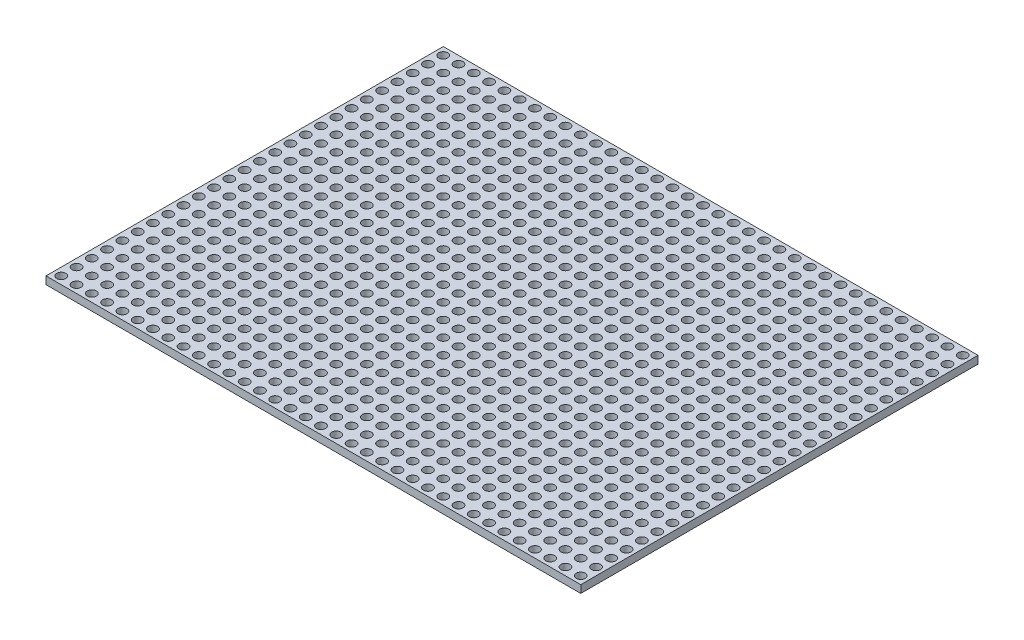
SolidWorks part; units mm, degrees
ref_plane "Front Plane" through (0, 0, 0) normal (0, 0, 1) x (1, 0, 0)
ref_plane "Top Plane" through (0, 0, 0) normal (0, 1, 0) x (1, 0, 0)
ref_plane "Right Plane" through (0, 0, 0) normal (1, 0, 0) x (0, 0, -1)
sketch "Sketch1" plane through (0, 0, 0) normal (0, 1, 0) x (1, 0, 0)
  line L1 (-35, -26) -> (35, -26)
  line L2 (-35, -26) -> (-35, 26)
  line L3 (-35, 26) -> (35, 26)
  line L4 (35, -26) -> (35, 26)
  line L5 (-35, -26) -> (35, 26) construction
  line L6 (-35, 26) -> (35, -26) construction
  circle A0 centre (-34, 25) radius 0.5928
  circle A1 centre (-32, 25) radius 0.5928
  circle A2 centre (-30, 25) radius 0.5928
  circle A3 centre (-28, 25) radius 0.5928
  circle A4 centre (-26, 25) radius 0.5928
  circle A5 centre (-24, 25) radius 0.5928
  circle A6 centre (-22, 25) radius 0.5928
  circle A7 centre (-20, 25) radius 0.5928
  circle A8 centre (-18, 25) radius 0.5928
  circle A9 centre (-16, 25) radius 0.5928
  circle A10 centre (-14, 25) radius 0.5928
  circle A11 centre (-12, 25) radius 0.5928
  circle A12 centre (-10, 25) radius 0.5928
  circle A13 centre (-8, 25) radius 0.5928
  circle A14 centre (-6, 25) radius 0.5928
  circle A15 centre (-4, 25) radius 0.5928
  circle A16 centre (-2, 25) radius 0.5928
  circle A17 centre (0, 25) radius 0.5928
  circle A18 centre (2, 25) radius 0.5928
  circle A19 centre (4, 25) radius 0.5928
  circle A20 centre (6, 25) radius 0.5928
  circle A21 centre (8, 25) radius 0.5928
  circle A22 centre (10, 25) radius 0.5928
  circle A23 centre (12, 25) radius 0.5928
  circle A24 centre (14, 25) radius 0.5928
  circle A25 centre (16, 25) radius 0.5928
  circle A26 centre (18, 25) radius 0.5928
  circle A27 centre (20, 25) radius 0.5928
  circle A28 centre (22, 25) radius 0.5928
  circle A29 centre (24, 25) radius 0.5928
  circle A30 centre (26, 25) radius 0.5928
  circle A31 centre (28, 25) radius 0.5928
  circle A32 centre (30, 25) radius 0.5928
  circle A33 centre (32, 25) radius 0.5928
  circle A34 centre (34, 25) radius 0.5928
  circle A35 centre (-32, 23) radius 0.5928
  circle A36 centre (-30, 23) radius 0.5928
  circle A37 centre (-28, 23) radius 0.5928
  circle A38 centre (-26, 23) radius 0.5928
  circle A39 centre (-24, 23) radius 0.5928
  circle A40 centre (-22, 23) radius 0.5928
  circle A41 centre (-20, 23) radius 0.5928
  circle A42 centre (-18, 23) radius 0.5928
  circle A43 centre (-16, 23) radius 0.5928
  circle A44 centre (-14, 23) radius 0.5928
  circle A45 centre (-12, 23) radius 0.5928
  circle A46 centre (-10, 23) radius 0.5928
  circle A47 centre (-8, 23) radius 0.5928
  circle A48 centre (-6, 23) radius 0.5928
  circle A49 centre (-4, 23) radius 0.5928
  circle A50 centre (-2, 23) radius 0.5928
  circle A51 centre (0, 23) radius 0.5928
  circle A52 centre (2, 23) radius 0.5928
  circle A53 centre (4, 23) radius 0.5928
  circle A54 centre (6, 23) radius 0.5928
  circle A55 centre (8, 23) radius 0.5928
  circle A56 centre (10, 23) radius 0.5928
  circle A57 centre (12, 23) radius 0.5928
  circle A58 centre (14, 23) radius 0.5928
  circle A59 centre (16, 23) radius 0.5928
  circle A60 centre (18, 23) radius 0.5928
  circle A61 centre (20, 23) radius 0.5928
  circle A62 centre (22, 23) radius 0.5928
  circle A63 centre (24, 23) radius 0.5928
  circle A64 centre (26, 23) radius 0.5928
  circle A65 centre (28, 23) radius 0.5928
  circle A66 centre (30, 23) radius 0.5928
  circle A67 centre (32, 23) radius 0.5928
  circle A68 centre (34, 23) radius 0.5928
  circle A69 centre (-32, 21) radius 0.5928
  circle A70 centre (-30, 21) radius 0.5928
  circle A71 centre (-28, 21) radius 0.5928
  circle A72 centre (-26, 21) radius 0.5928
  circle A73 centre (-24, 21) radius 0.5928
  circle A74 centre (-22, 21) radius 0.5928
  circle A75 centre (-20, 21) radius 0.5928
  circle A76 centre (-18, 21) radius 0.5928
  circle A77 centre (-16, 21) radius 0.5928
  circle A78 centre (-14, 21) radius 0.5928
  circle A79 centre (-12, 21) radius 0.5928
  circle A80 centre (-10, 21) radius 0.5928
  circle A81 centre (-8, 21) radius 0.5928
  circle A82 centre (-6, 21) radius 0.5928
  circle A83 centre (-4, 21) radius 0.5928
  circle A84 centre (-2, 21) radius 0.5928
  circle A85 centre (0, 21) radius 0.5928
  circle A86 centre (2, 21) radius 0.5928
  circle A87 centre (4, 21) radius 0.5928
  circle A88 centre (6, 21) radius 0.5928
  circle A89 centre (8, 21) radius 0.5928
  circle A90 centre (10, 21) radius 0.5928
  circle A91 centre (12, 21) radius 0.5928
  circle A92 centre (14, 21) radius 0.5928
  circle A93 centre (16, 21) radius 0.5928
  circle A94 centre (18, 21) radius 0.5928
  circle A95 centre (20, 21) radius 0.5928
  circle A96 centre (22, 21) radius 0.5928
  circle A97 centre (24, 21) radius 0.5928
  circle A98 centre (26, 21) radius 0.5928
  circle A99 centre (28, 21) radius 0.5928
  circle A100 centre (30, 21) radius 0.5928
  circle A101 centre (32, 21) radius 0.5928
  circle A102 centre (34, 21) radius 0.5928
  circle A103 centre (-32, 19) radius 0.5928
  circle A104 centre (-30, 19) radius 0.5928
  circle A105 centre (-28, 19) radius 0.5928
  circle A106 centre (-26, 19) radius 0.5928
  circle A107 centre (-24, 19) radius 0.5928
  circle A108 centre (-22, 19) radius 0.5928
  circle A109 centre (-20, 19) radius 0.5928
  circle A110 centre (-18, 19) radius 0.5928
  circle A111 centre (-16, 19) radius 0.5928
  circle A112 centre (-14, 19) radius 0.5928
  circle A113 centre (-12, 19) radius 0.5928
  circle A114 centre (-10, 19) radius 0.5928
  circle A115 centre (-8, 19) radius 0.5928
  circle A116 centre (-6, 19) radius 0.5928
  circle A117 centre (-4, 19) radius 0.5928
  circle A118 centre (-2, 19) radius 0.5928
  circle A119 centre (0, 19) radius 0.5928
  circle A120 centre (2, 19) radius 0.5928
  circle A121 centre (4, 19) radius 0.5928
  circle A122 centre (6, 19) radius 0.5928
  circle A123 centre (8, 19) radius 0.5928
  circle A124 centre (10, 19) radius 0.5928
  circle A125 centre (12, 19) radius 0.5928
  circle A126 centre (14, 19) radius 0.5928
  circle A127 centre (16, 19) radius 0.5928
  circle A128 centre (18, 19) radius 0.5928
  circle A129 centre (20, 19) radius 0.5928
  circle A130 centre (22, 19) radius 0.5928
  circle A131 centre (24, 19) radius 0.5928
  circle A132 centre (26, 19) radius 0.5928
  circle A133 centre (28, 19) radius 0.5928
  circle A134 centre (30, 19) radius 0.5928
  circle A135 centre (32, 19) radius 0.5928
  circle A136 centre (34, 19) radius 0.5928
  circle A137 centre (-32, 17) radius 0.5928
  circle A138 centre (-30, 17) radius 0.5928
  circle A139 centre (-28, 17) radius 0.5928
  circle A140 centre (-26, 17) radius 0.5928
  circle A141 centre (-24, 17) radius 0.5928
  circle A142 centre (-22, 17) radius 0.5928
  circle A143 centre (-20, 17) radius 0.5928
  circle A144 centre (-18, 17) radius 0.5928
  circle A145 centre (-16, 17) radius 0.5928
  circle A146 centre (-14, 17) radius 0.5928
  circle A147 centre (-12, 17) radius 0.5928
  circle A148 centre (-10, 17) radius 0.5928
  circle A149 centre (-8, 17) radius 0.5928
  circle A150 centre (-6, 17) radius 0.5928
  circle A151 centre (-4, 17) radius 0.5928
  circle A152 centre (-2, 17) radius 0.5928
  circle A153 centre (0, 17) radius 0.5928
  circle A154 centre (2, 17) radius 0.5928
  circle A155 centre (4, 17) radius 0.5928
  circle A156 centre (6, 17) radius 0.5928
  circle A157 centre (8, 17) radius 0.5928
  circle A158 centre (10, 17) radius 0.5928
  circle A159 centre (12, 17) radius 0.5928
  circle A160 centre (14, 17) radius 0.5928
  circle A161 centre (16, 17) radius 0.5928
  circle A162 centre (18, 17) radius 0.5928
  circle A163 centre (20, 17) radius 0.5928
  circle A164 centre (22, 17) radius 0.5928
  circle A165 centre (24, 17) radius 0.5928
  circle A166 centre (26, 17) radius 0.5928
  circle A167 centre (28, 17) radius 0.5928
  circle A168 centre (30, 17) radius 0.5928
  circle A169 centre (32, 17) radius 0.5928
  circle A170 centre (34, 17) radius 0.5928
  circle A171 centre (-32, 15) radius 0.5928
  circle A172 centre (-30, 15) radius 0.5928
  circle A173 centre (-28, 15) radius 0.5928
  circle A174 centre (-26, 15) radius 0.5928
  circle A175 centre (-24, 15) radius 0.5928
  circle A176 centre (-22, 15) radius 0.5928
  circle A177 centre (-20, 15) radius 0.5928
  circle A178 centre (-18, 15) radius 0.5928
  circle A179 centre (-16, 15) radius 0.5928
  circle A180 centre (-14, 15) radius 0.5928
  circle A181 centre (-12, 15) radius 0.5928
  circle A182 centre (-10, 15) radius 0.5928
  circle A183 centre (-8, 15) radius 0.5928
  circle A184 centre (-6, 15) radius 0.5928
  circle A185 centre (-4, 15) radius 0.5928
  circle A186 centre (-2, 15) radius 0.5928
  circle A187 centre (0, 15) radius 0.5928
  circle A188 centre (2, 15) radius 0.5928
  circle A189 centre (4, 15) radius 0.5928
  circle A190 centre (6, 15) radius 0.5928
  circle A191 centre (8, 15) radius 0.5928
  circle A192 centre (10, 15) radius 0.5928
  circle A193 centre (12, 15) radius 0.5928
  circle A194 centre (14, 15) radius 0.5928
  circle A195 centre (16, 15) radius 0.5928
  circle A196 centre (18, 15) radius 0.5928
  circle A197 centre (20, 15) radius 0.5928
  circle A198 centre (22, 15) radius 0.5928
  circle A199 centre (24, 15) radius 0.5928
  circle A200 centre (26, 15) radius 0.5928
  circle A201 centre (28, 15) radius 0.5928
  circle A202 centre (30, 15) radius 0.5928
  circle A203 centre (32, 15) radius 0.5928
  circle A204 centre (34, 15) radius 0.5928
  circle A205 centre (-32, 13) radius 0.5928
  circle A206 centre (-30, 13) radius 0.5928
  circle A207 centre (-28, 13) radius 0.5928
  circle A208 centre (-26, 13) radius 0.5928
  circle A209 centre (-24, 13) radius 0.5928
  circle A210 centre (-22, 13) radius 0.5928
  circle A211 centre (-20, 13) radius 0.5928
  circle A212 centre (-18, 13) radius 0.5928
  circle A213 centre (-16, 13) radius 0.5928
  circle A214 centre (-14, 13) radius 0.5928
  circle A215 centre (-12, 13) radius 0.5928
  circle A216 centre (-10, 13) radius 0.5928
  circle A217 centre (-8, 13) radius 0.5928
  circle A218 centre (-6, 13) radius 0.5928
  circle A219 centre (-4, 13) radius 0.5928
  circle A220 centre (-2, 13) radius 0.5928
  circle A221 centre (0, 13) radius 0.5928
  circle A222 centre (2, 13) radius 0.5928
  circle A223 centre (4, 13) radius 0.5928
  circle A224 centre (6, 13) radius 0.5928
  circle A225 centre (8, 13) radius 0.5928
  circle A226 centre (10, 13) radius 0.5928
  circle A227 centre (12, 13) radius 0.5928
  circle A228 centre (14, 13) radius 0.5928
  circle A229 centre (16, 13) radius 0.5928
  circle A230 centre (18, 13) radius 0.5928
  circle A231 centre (20, 13) radius 0.5928
  circle A232 centre (22, 13) radius 0.5928
  circle A233 centre (24, 13) radius 0.5928
  circle A234 centre (26, 13) radius 0.5928
  circle A235 centre (28, 13) radius 0.5928
  circle A236 centre (30, 13) radius 0.5928
  circle A237 centre (32, 13) radius 0.5928
  circle A238 centre (34, 13) radius 0.5928
  circle A239 centre (-32, 11) radius 0.5928
  circle A240 centre (-30, 11) radius 0.5928
  circle A241 centre (-28, 11) radius 0.5928
  circle A242 centre (-26, 11) radius 0.5928
  circle A243 centre (-24, 11) radius 0.5928
  circle A244 centre (-22, 11) radius 0.5928
  circle A245 centre (-20, 11) radius 0.5928
  circle A246 centre (-18, 11) radius 0.5928
  circle A247 centre (-16, 11) radius 0.5928
  circle A248 centre (-14, 11) radius 0.5928
  circle A249 centre (-12, 11) radius 0.5928
  circle A250 centre (-10, 11) radius 0.5928
  circle A251 centre (-8, 11) radius 0.5928
  circle A252 centre (-6, 11) radius 0.5928
  circle A253 centre (-4, 11) radius 0.5928
  circle A254 centre (-2, 11) radius 0.5928
  circle A255 centre (0, 11) radius 0.5928
  circle A256 centre (2, 11) radius 0.5928
  circle A257 centre (4, 11) radius 0.5928
  circle A258 centre (6, 11) radius 0.5928
  circle A259 centre (8, 11) radius 0.5928
  circle A260 centre (10, 11) radius 0.5928
  circle A261 centre (12, 11) radius 0.5928
  circle A262 centre (14, 11) radius 0.5928
  circle A263 centre (16, 11) radius 0.5928
  circle A264 centre (18, 11) radius 0.5928
  circle A265 centre (20, 11) radius 0.5928
  circle A266 centre (22, 11) radius 0.5928
  circle A267 centre (24, 11) radius 0.5928
  circle A268 centre (26, 11) radius 0.5928
  circle A269 centre (28, 11) radius 0.5928
  circle A270 centre (30, 11) radius 0.5928
  circle A271 centre (32, 11) radius 0.5928
  circle A272 centre (34, 11) radius 0.5928
  circle A273 centre (-32, 9) radius 0.5928
  circle A274 centre (-30, 9) radius 0.5928
  circle A275 centre (-28, 9) radius 0.5928
  circle A276 centre (-26, 9) radius 0.5928
  circle A277 centre (-24, 9) radius 0.5928
  circle A278 centre (-22, 9) radius 0.5928
  circle A279 centre (-20, 9) radius 0.5928
  circle A280 centre (-18, 9) radius 0.5928
  circle A281 centre (-16, 9) radius 0.5928
  circle A282 centre (-14, 9) radius 0.5928
  circle A283 centre (-12, 9) radius 0.5928
  circle A284 centre (-10, 9) radius 0.5928
  circle A285 centre (-8, 9) radius 0.5928
  circle A286 centre (-6, 9) radius 0.5928
  circle A287 centre (-4, 9) radius 0.5928
  circle A288 centre (-2, 9) radius 0.5928
  circle A289 centre (0, 9) radius 0.5928
  circle A290 centre (2, 9) radius 0.5928
  circle A291 centre (4, 9) radius 0.5928
  circle A292 centre (6, 9) radius 0.5928
  circle A293 centre (8, 9) radius 0.5928
  circle A294 centre (10, 9) radius 0.5928
  circle A295 centre (12, 9) radius 0.5928
  circle A296 centre (14, 9) radius 0.5928
  circle A297 centre (16, 9) radius 0.5928
  circle A298 centre (18, 9) radius 0.5928
  circle A299 centre (20, 9) radius 0.5928
  circle A300 centre (22, 9) radius 0.5928
  circle A301 centre (24, 9) radius 0.5928
  circle A302 centre (26, 9) radius 0.5928
  circle A303 centre (28, 9) radius 0.5928
  circle A304 centre (30, 9) radius 0.5928
  circle A305 centre (32, 9) radius 0.5928
  circle A306 centre (34, 9) radius 0.5928
  circle A307 centre (-32, 7) radius 0.5928
  circle A308 centre (-30, 7) radius 0.5928
  circle A309 centre (-28, 7) radius 0.5928
  circle A310 centre (-26, 7) radius 0.5928
  circle A311 centre (-24, 7) radius 0.5928
  circle A312 centre (-22, 7) radius 0.5928
  circle A313 centre (-20, 7) radius 0.5928
  circle A314 centre (-18, 7) radius 0.5928
  circle A315 centre (-16, 7) radius 0.5928
  circle A316 centre (-14, 7) radius 0.5928
  circle A317 centre (-12, 7) radius 0.5928
  circle A318 centre (-10, 7) radius 0.5928
  circle A319 centre (-8, 7) radius 0.5928
  circle A320 centre (-6, 7) radius 0.5928
  circle A321 centre (-4, 7) radius 0.5928
  circle A322 centre (-2, 7) radius 0.5928
  circle A323 centre (0, 7) radius 0.5928
  circle A324 centre (2, 7) radius 0.5928
  circle A325 centre (4, 7) radius 0.5928
  circle A326 centre (6, 7) radius 0.5928
  circle A327 centre (8, 7) radius 0.5928
  circle A328 centre (10, 7) radius 0.5928
  circle A329 centre (12, 7) radius 0.5928
  circle A330 centre (14, 7) radius 0.5928
  circle A331 centre (16, 7) radius 0.5928
  circle A332 centre (18, 7) radius 0.5928
  circle A333 centre (20, 7) radius 0.5928
  circle A334 centre (22, 7) radius 0.5928
  circle A335 centre (24, 7) radius 0.5928
  circle A336 centre (26, 7) radius 0.5928
  circle A337 centre (28, 7) radius 0.5928
  circle A338 centre (30, 7) radius 0.5928
  circle A339 centre (32, 7) radius 0.5928
  circle A340 centre (34, 7) radius 0.5928
  circle A341 centre (-32, 5) radius 0.5928
  circle A342 centre (-30, 5) radius 0.5928
  circle A343 centre (-28, 5) radius 0.5928
  circle A344 centre (-26, 5) radius 0.5928
  circle A345 centre (-24, 5) radius 0.5928
  circle A346 centre (-22, 5) radius 0.5928
  circle A347 centre (-20, 5) radius 0.5928
  circle A348 centre (-18, 5) radius 0.5928
  circle A349 centre (-16, 5) radius 0.5928
  circle A350 centre (-14, 5) radius 0.5928
  circle A351 centre (-12, 5) radius 0.5928
  circle A352 centre (-10, 5) radius 0.5928
  circle A353 centre (-8, 5) radius 0.5928
  circle A354 centre (-6, 5) radius 0.5928
  circle A355 centre (-4, 5) radius 0.5928
  circle A356 centre (-2, 5) radius 0.5928
  circle A357 centre (0, 5) radius 0.5928
  circle A358 centre (2, 5) radius 0.5928
  circle A359 centre (4, 5) radius 0.5928
  circle A360 centre (6, 5) radius 0.5928
  circle A361 centre (8, 5) radius 0.5928
  circle A362 centre (10, 5) radius 0.5928
  circle A363 centre (12, 5) radius 0.5928
  circle A364 centre (14, 5) radius 0.5928
  circle A365 centre (16, 5) radius 0.5928
  circle A366 centre (18, 5) radius 0.5928
  circle A367 centre (20, 5) radius 0.5928
  circle A368 centre (22, 5) radius 0.5928
  circle A369 centre (24, 5) radius 0.5928
  circle A370 centre (26, 5) radius 0.5928
  circle A371 centre (28, 5) radius 0.5928
  circle A372 centre (30, 5) radius 0.5928
  circle A373 centre (32, 5) radius 0.5928
  circle A374 centre (34, 5) radius 0.5928
  circle A375 centre (-32, 3) radius 0.5928
  circle A376 centre (-30, 3) radius 0.5928
  circle A377 centre (-28, 3) radius 0.5928
  circle A378 centre (-26, 3) radius 0.5928
  circle A379 centre (-24, 3) radius 0.5928
  circle A380 centre (-22, 3) radius 0.5928
  circle A381 centre (-20, 3) radius 0.5928
  circle A382 centre (-18, 3) radius 0.5928
  circle A383 centre (-16, 3) radius 0.5928
  circle A384 centre (-14, 3) radius 0.5928
  circle A385 centre (-12, 3) radius 0.5928
  circle A386 centre (-10, 3) radius 0.5928
  circle A387 centre (-8, 3) radius 0.5928
  circle A388 centre (-6, 3) radius 0.5928
  circle A389 centre (-4, 3) radius 0.5928
  circle A390 centre (-2, 3) radius 0.5928
  circle A391 centre (0, 3) radius 0.5928
  circle A392 centre (2, 3) radius 0.5928
  circle A393 centre (4, 3) radius 0.5928
  circle A394 centre (6, 3) radius 0.5928
  circle A395 centre (8, 3) radius 0.5928
  circle A396 centre (10, 3) radius 0.5928
  circle A397 centre (12, 3) radius 0.5928
  circle A398 centre (14, 3) radius 0.5928
  circle A399 centre (16, 3) radius 0.5928
  circle A400 centre (18, 3) radius 0.5928
  circle A401 centre (20, 3) radius 0.5928
  circle A402 centre (22, 3) radius 0.5928
  circle A403 centre (24, 3) radius 0.5928
  circle A404 centre (26, 3) radius 0.5928
  circle A405 centre (28, 3) radius 0.5928
  circle A406 centre (30, 3) radius 0.5928
  circle A407 centre (32, 3) radius 0.5928
  circle A408 centre (34, 3) radius 0.5928
  circle A409 centre (-32, 1) radius 0.5928
  circle A410 centre (-30, 1) radius 0.5928
  circle A411 centre (-28, 1) radius 0.5928
  circle A412 centre (-26, 1) radius 0.5928
  circle A413 centre (-24, 1) radius 0.5928
  circle A414 centre (-22, 1) radius 0.5928
  circle A415 centre (-20, 1) radius 0.5928
  circle A416 centre (-18, 1) radius 0.5928
  circle A417 centre (-16, 1) radius 0.5928
  circle A418 centre (-14, 1) radius 0.5928
  circle A419 centre (-12, 1) radius 0.5928
  circle A420 centre (-10, 1) radius 0.5928
  circle A421 centre (-8, 1) radius 0.5928
  circle A422 centre (-6, 1) radius 0.5928
  circle A423 centre (-4, 1) radius 0.5928
  circle A424 centre (-2, 1) radius 0.5928
  circle A425 centre (0, 1) radius 0.5928
  circle A426 centre (2, 1) radius 0.5928
  circle A427 centre (4, 1) radius 0.5928
  circle A428 centre (6, 1) radius 0.5928
  circle A429 centre (8, 1) radius 0.5928
  circle A430 centre (10, 1) radius 0.5928
  circle A431 centre (12, 1) radius 0.5928
  circle A432 centre (14, 1) radius 0.5928
  circle A433 centre (16, 1) radius 0.5928
  circle A434 centre (18, 1) radius 0.5928
  circle A435 centre (20, 1) radius 0.5928
  circle A436 centre (22, 1) radius 0.5928
  circle A437 centre (24, 1) radius 0.5928
  circle A438 centre (26, 1) radius 0.5928
  circle A439 centre (28, 1) radius 0.5928
  circle A440 centre (30, 1) radius 0.5928
  circle A441 centre (32, 1) radius 0.5928
  circle A442 centre (34, 1) radius 0.5928
  circle A443 centre (-32, -1) radius 0.5928
  circle A444 centre (-30, -1) radius 0.5928
  circle A445 centre (-28, -1) radius 0.5928
  circle A446 centre (-26, -1) radius 0.5928
  circle A447 centre (-24, -1) radius 0.5928
  circle A448 centre (-22, -1) radius 0.5928
  circle A449 centre (-20, -1) radius 0.5928
  circle A450 centre (-18, -1) radius 0.5928
  circle A451 centre (-16, -1) radius 0.5928
  circle A452 centre (-14, -1) radius 0.5928
  circle A453 centre (-12, -1) radius 0.5928
  circle A454 centre (-10, -1) radius 0.5928
  circle A455 centre (-8, -1) radius 0.5928
  circle A456 centre (-6, -1) radius 0.5928
  circle A457 centre (-4, -1) radius 0.5928
  circle A458 centre (-2, -1) radius 0.5928
  circle A459 centre (0, -1) radius 0.5928
  circle A460 centre (2, -1) radius 0.5928
  circle A461 centre (4, -1) radius 0.5928
  circle A462 centre (6, -1) radius 0.5928
  circle A463 centre (8, -1) radius 0.5928
  circle A464 centre (10, -1) radius 0.5928
  circle A465 centre (12, -1) radius 0.5928
  circle A466 centre (14, -1) radius 0.5928
  circle A467 centre (16, -1) radius 0.5928
  circle A468 centre (18, -1) radius 0.5928
  circle A469 centre (20, -1) radius 0.5928
  circle A470 centre (22, -1) radius 0.5928
  circle A471 centre (24, -1) radius 0.5928
  circle A472 centre (26, -1) radius 0.5928
  circle A473 centre (28, -1) radius 0.5928
  circle A474 centre (30, -1) radius 0.5928
  circle A475 centre (32, -1) radius 0.5928
  circle A476 centre (34, -1) radius 0.5928
  circle A477 centre (-32, -3) radius 0.5928
  circle A478 centre (-30, -3) radius 0.5928
  circle A479 centre (-28, -3) radius 0.5928
  circle A480 centre (-26, -3) radius 0.5928
  circle A481 centre (-24, -3) radius 0.5928
  circle A482 centre (-22, -3) radius 0.5928
  circle A483 centre (-20, -3) radius 0.5928
  circle A484 centre (-18, -3) radius 0.5928
  circle A485 centre (-16, -3) radius 0.5928
  circle A486 centre (-14, -3) radius 0.5928
  circle A487 centre (-12, -3) radius 0.5928
  circle A488 centre (-10, -3) radius 0.5928
  circle A489 centre (-8, -3) radius 0.5928
  circle A490 centre (-6, -3) radius 0.5928
  circle A491 centre (-4, -3) radius 0.5928
  circle A492 centre (-2, -3) radius 0.5928
  circle A493 centre (0, -3) radius 0.5928
  circle A494 centre (2, -3) radius 0.5928
  circle A495 centre (4, -3) radius 0.5928
  circle A496 centre (6, -3) radius 0.5928
  circle A497 centre (8, -3) radius 0.5928
  circle A498 centre (10, -3) radius 0.5928
  circle A499 centre (12, -3) radius 0.5928
  circle A500 centre (14, -3) radius 0.5928
  circle A501 centre (16, -3) radius 0.5928
  circle A502 centre (18, -3) radius 0.5928
  circle A503 centre (20, -3) radius 0.5928
  circle A504 centre (22, -3) radius 0.5928
  circle A505 centre (24, -3) radius 0.5928
  circle A506 centre (26, -3) radius 0.5928
  circle A507 centre (28, -3) radius 0.5928
  circle A508 centre (30, -3) radius 0.5928
  circle A509 centre (32, -3) radius 0.5928
  circle A510 centre (34, -3) radius 0.5928
  circle A511 centre (-32, -5) radius 0.5928
  circle A512 centre (-30, -5) radius 0.5928
  circle A513 centre (-28, -5) radius 0.5928
  circle A514 centre (-26, -5) radius 0.5928
  circle A515 centre (-24, -5) radius 0.5928
  circle A516 centre (-22, -5) radius 0.5928
  circle A517 centre (-20, -5) radius 0.5928
  circle A518 centre (-18, -5) radius 0.5928
  circle A519 centre (-16, -5) radius 0.5928
  circle A520 centre (-14, -5) radius 0.5928
  circle A521 centre (-12, -5) radius 0.5928
  circle A522 centre (-10, -5) radius 0.5928
  circle A523 centre (-8, -5) radius 0.5928
  circle A524 centre (-6, -5) radius 0.5928
  circle A525 centre (-4, -5) radius 0.5928
  circle A526 centre (-2, -5) radius 0.5928
  circle A527 centre (0, -5) radius 0.5928
  circle A528 centre (2, -5) radius 0.5928
  circle A529 centre (4, -5) radius 0.5928
  circle A530 centre (6, -5) radius 0.5928
  circle A531 centre (8, -5) radius 0.5928
  circle A532 centre (10, -5) radius 0.5928
  circle A533 centre (12, -5) radius 0.5928
  circle A534 centre (14, -5) radius 0.5928
  circle A535 centre (16, -5) radius 0.5928
  circle A536 centre (18, -5) radius 0.5928
  circle A537 centre (20, -5) radius 0.5928
  circle A538 centre (22, -5) radius 0.5928
  circle A539 centre (24, -5) radius 0.5928
  circle A540 centre (26, -5) radius 0.5928
  circle A541 centre (28, -5) radius 0.5928
  circle A542 centre (30, -5) radius 0.5928
  circle A543 centre (32, -5) radius 0.5928
  circle A544 centre (34, -5) radius 0.5928
  circle A545 centre (-32, -7) radius 0.5928
  circle A546 centre (-30, -7) radius 0.5928
  circle A547 centre (-28, -7) radius 0.5928
  circle A548 centre (-26, -7) radius 0.5928
  circle A549 centre (-24, -7) radius 0.5928
  circle A550 centre (-22, -7) radius 0.5928
  circle A551 centre (-20, -7) radius 0.5928
  circle A552 centre (-18, -7) radius 0.5928
  circle A553 centre (-16, -7) radius 0.5928
  circle A554 centre (-14, -7) radius 0.5928
  circle A555 centre (-12, -7) radius 0.5928
  circle A556 centre (-10, -7) radius 0.5928
  circle A557 centre (-8, -7) radius 0.5928
  circle A558 centre (-6, -7) radius 0.5928
  circle A559 centre (-4, -7) radius 0.5928
  circle A560 centre (-2, -7) radius 0.5928
  circle A561 centre (0, -7) radius 0.5928
  circle A562 centre (2, -7) radius 0.5928
  circle A563 centre (4, -7) radius 0.5928
  circle A564 centre (6, -7) radius 0.5928
  circle A565 centre (8, -7) radius 0.5928
  circle A566 centre (10, -7) radius 0.5928
  circle A567 centre (12, -7) radius 0.5928
  circle A568 centre (14, -7) radius 0.5928
  circle A569 centre (16, -7) radius 0.5928
  circle A570 centre (18, -7) radius 0.5928
  circle A571 centre (20, -7) radius 0.5928
  circle A572 centre (22, -7) radius 0.5928
  circle A573 centre (24, -7) radius 0.5928
  circle A574 centre (26, -7) radius 0.5928
  circle A575 centre (28, -7) radius 0.5928
  circle A576 centre (30, -7) radius 0.5928
  circle A577 centre (32, -7) radius 0.5928
  circle A578 centre (34, -7) radius 0.5928
  circle A579 centre (-32, -9) radius 0.5928
  circle A580 centre (-30, -9) radius 0.5928
  circle A581 centre (-28, -9) radius 0.5928
  circle A582 centre (-26, -9) radius 0.5928
  circle A583 centre (-24, -9) radius 0.5928
  circle A584 centre (-22, -9) radius 0.5928
  circle A585 centre (-20, -9) radius 0.5928
  circle A586 centre (-18, -9) radius 0.5928
  circle A587 centre (-16, -9) radius 0.5928
  circle A588 centre (-14, -9) radius 0.5928
  circle A589 centre (-12, -9) radius 0.5928
  circle A590 centre (-10, -9) radius 0.5928
  circle A591 centre (-8, -9) radius 0.5928
  circle A592 centre (-6, -9) radius 0.5928
  circle A593 centre (-4, -9) radius 0.5928
  circle A594 centre (-2, -9) radius 0.5928
  circle A595 centre (0, -9) radius 0.5928
  circle A596 centre (2, -9) radius 0.5928
  circle A597 centre (4, -9) radius 0.5928
  circle A598 centre (6, -9) radius 0.5928
  circle A599 centre (8, -9) radius 0.5928
  circle A600 centre (10, -9) radius 0.5928
  circle A601 centre (12, -9) radius 0.5928
  circle A602 centre (14, -9) radius 0.5928
  circle A603 centre (16, -9) radius 0.5928
  circle A604 centre (18, -9) radius 0.5928
  circle A605 centre (20, -9) radius 0.5928
  circle A606 centre (22, -9) radius 0.5928
  circle A607 centre (24, -9) radius 0.5928
  circle A608 centre (26, -9) radius 0.5928
  circle A609 centre (28, -9) radius 0.5928
  circle A610 centre (30, -9) radius 0.5928
  circle A611 centre (32, -9) radius 0.5928
  circle A612 centre (34, -9) radius 0.5928
  circle A613 centre (-32, -11) radius 0.5928
  circle A614 centre (-30, -11) radius 0.5928
  circle A615 centre (-28, -11) radius 0.5928
  circle A616 centre (-26, -11) radius 0.5928
  circle A617 centre (-24, -11) radius 0.5928
  circle A618 centre (-22, -11) radius 0.5928
  circle A619 centre (-20, -11) radius 0.5928
  circle A620 centre (-18, -11) radius 0.5928
  circle A621 centre (-16, -11) radius 0.5928
  circle A622 centre (-14, -11) radius 0.5928
  circle A623 centre (-12, -11) radius 0.5928
  circle A624 centre (-10, -11) radius 0.5928
  circle A625 centre (-8, -11) radius 0.5928
  circle A626 centre (-6, -11) radius 0.5928
  circle A627 centre (-4, -11) radius 0.5928
  circle A628 centre (-2, -11) radius 0.5928
  circle A629 centre (0, -11) radius 0.5928
  circle A630 centre (2, -11) radius 0.5928
  circle A631 centre (4, -11) radius 0.5928
  circle A632 centre (6, -11) radius 0.5928
  circle A633 centre (8, -11) radius 0.5928
  circle A634 centre (10, -11) radius 0.5928
  circle A635 centre (12, -11) radius 0.5928
  circle A636 centre (14, -11) radius 0.5928
  circle A637 centre (16, -11) radius 0.5928
  circle A638 centre (18, -11) radius 0.5928
  circle A639 centre (20, -11) radius 0.5928
  circle A640 centre (22, -11) radius 0.5928
  circle A641 centre (24, -11) radius 0.5928
  circle A642 centre (26, -11) radius 0.5928
  circle A643 centre (28, -11) radius 0.5928
  circle A644 centre (30, -11) radius 0.5928
  circle A645 centre (32, -11) radius 0.5928
  circle A646 centre (34, -11) radius 0.5928
  circle A647 centre (-32, -13) radius 0.5928
  circle A648 centre (-30, -13) radius 0.5928
  circle A649 centre (-28, -13) radius 0.5928
  circle A650 centre (-26, -13) radius 0.5928
  circle A651 centre (-24, -13) radius 0.5928
  circle A652 centre (-22, -13) radius 0.5928
  circle A653 centre (-20, -13) radius 0.5928
  circle A654 centre (-18, -13) radius 0.5928
  circle A655 centre (-16, -13) radius 0.5928
  circle A656 centre (-14, -13) radius 0.5928
  circle A657 centre (-12, -13) radius 0.5928
  circle A658 centre (-10, -13) radius 0.5928
  circle A659 centre (-8, -13) radius 0.5928
  circle A660 centre (-6, -13) radius 0.5928
  circle A661 centre (-4, -13) radius 0.5928
  circle A662 centre (-2, -13) radius 0.5928
  circle A663 centre (0, -13) radius 0.5928
  circle A664 centre (2, -13) radius 0.5928
  circle A665 centre (4, -13) radius 0.5928
  circle A666 centre (6, -13) radius 0.5928
  circle A667 centre (8, -13) radius 0.5928
  circle A668 centre (10, -13) radius 0.5928
  circle A669 centre (12, -13) radius 0.5928
  circle A670 centre (14, -13) radius 0.5928
  circle A671 centre (16, -13) radius 0.5928
  circle A672 centre (18, -13) radius 0.5928
  circle A673 centre (20, -13) radius 0.5928
  circle A674 centre (22, -13) radius 0.5928
  circle A675 centre (24, -13) radius 0.5928
  circle A676 centre (26, -13) radius 0.5928
  circle A677 centre (28, -13) radius 0.5928
  circle A678 centre (30, -13) radius 0.5928
  circle A679 centre (32, -13) radius 0.5928
  circle A680 centre (34, -13) radius 0.5928
  circle A681 centre (-32, -15) radius 0.5928
  circle A682 centre (-30, -15) radius 0.5928
  circle A683 centre (-28, -15) radius 0.5928
  circle A684 centre (-26, -15) radius 0.5928
  circle A685 centre (-24, -15) radius 0.5928
  circle A686 centre (-22, -15) radius 0.5928
  circle A687 centre (-20, -15) radius 0.5928
  circle A688 centre (-18, -15) radius 0.5928
  circle A689 centre (-16, -15) radius 0.5928
  circle A690 centre (-14, -15) radius 0.5928
  circle A691 centre (-12, -15) radius 0.5928
  circle A692 centre (-10, -15) radius 0.5928
  circle A693 centre (-8, -15) radius 0.5928
  circle A694 centre (-6, -15) radius 0.5928
  circle A695 centre (-4, -15) radius 0.5928
  circle A696 centre (-2, -15) radius 0.5928
  circle A697 centre (0, -15) radius 0.5928
  circle A698 centre (2, -15) radius 0.5928
  circle A699 centre (4, -15) radius 0.5928
  circle A700 centre (6, -15) radius 0.5928
  circle A701 centre (8, -15) radius 0.5928
  circle A702 centre (10, -15) radius 0.5928
  circle A703 centre (12, -15) radius 0.5928
  circle A704 centre (14, -15) radius 0.5928
  circle A705 centre (16, -15) radius 0.5928
  circle A706 centre (18, -15) radius 0.5928
  circle A707 centre (20, -15) radius 0.5928
  circle A708 centre (22, -15) radius 0.5928
  circle A709 centre (24, -15) radius 0.5928
  circle A710 centre (26, -15) radius 0.5928
  circle A711 centre (28, -15) radius 0.5928
  circle A712 centre (30, -15) radius 0.5928
  circle A713 centre (32, -15) radius 0.5928
  circle A714 centre (34, -15) radius 0.5928
  circle A715 centre (-32, -17) radius 0.5928
  circle A716 centre (-30, -17) radius 0.5928
  circle A717 centre (-28, -17) radius 0.5928
  circle A718 centre (-26, -17) radius 0.5928
  circle A719 centre (-24, -17) radius 0.5928
  circle A720 centre (-22, -17) radius 0.5928
  circle A721 centre (-20, -17) radius 0.5928
  circle A722 centre (-18, -17) radius 0.5928
  circle A723 centre (-16, -17) radius 0.5928
  circle A724 centre (-14, -17) radius 0.5928
  circle A725 centre (-12, -17) radius 0.5928
  circle A726 centre (-10, -17) radius 0.5928
  circle A727 centre (-8, -17) radius 0.5928
  circle A728 centre (-6, -17) radius 0.5928
  circle A729 centre (-4, -17) radius 0.5928
  circle A730 centre (-2, -17) radius 0.5928
  circle A731 centre (0, -17) radius 0.5928
  circle A732 centre (2, -17) radius 0.5928
  circle A733 centre (4, -17) radius 0.5928
  circle A734 centre (6, -17) radius 0.5928
  circle A735 centre (8, -17) radius 0.5928
  circle A736 centre (10, -17) radius 0.5928
  circle A737 centre (12, -17) radius 0.5928
  circle A738 centre (14, -17) radius 0.5928
  circle A739 centre (16, -17) radius 0.5928
  circle A740 centre (18, -17) radius 0.5928
  circle A741 centre (20, -17) radius 0.5928
  circle A742 centre (22, -17) radius 0.5928
  circle A743 centre (24, -17) radius 0.5928
  circle A744 centre (26, -17) radius 0.5928
  circle A745 centre (28, -17) radius 0.5928
  circle A746 centre (30, -17) radius 0.5928
  circle A747 centre (32, -17) radius 0.5928
  circle A748 centre (34, -17) radius 0.5928
  circle A749 centre (-32, -19) radius 0.5928
  circle A750 centre (-30, -19) radius 0.5928
  circle A751 centre (-28, -19) radius 0.5928
  circle A752 centre (-26, -19) radius 0.5928
  circle A753 centre (-24, -19) radius 0.5928
  circle A754 centre (-22, -19) radius 0.5928
  circle A755 centre (-20, -19) radius 0.5928
  circle A756 centre (-18, -19) radius 0.5928
  circle A757 centre (-16, -19) radius 0.5928
  circle A758 centre (-14, -19) radius 0.5928
  circle A759 centre (-12, -19) radius 0.5928
  circle A760 centre (-10, -19) radius 0.5928
  circle A761 centre (-8, -19) radius 0.5928
  circle A762 centre (-6, -19) radius 0.5928
  circle A763 centre (-4, -19) radius 0.5928
  circle A764 centre (-2, -19) radius 0.5928
  circle A765 centre (0, -19) radius 0.5928
  circle A766 centre (2, -19) radius 0.5928
  circle A767 centre (4, -19) radius 0.5928
  circle A768 centre (6, -19) radius 0.5928
  circle A769 centre (8, -19) radius 0.5928
  circle A770 centre (10, -19) radius 0.5928
  circle A771 centre (12, -19) radius 0.5928
  circle A772 centre (14, -19) radius 0.5928
  circle A773 centre (16, -19) radius 0.5928
  circle A774 centre (18, -19) radius 0.5928
  circle A775 centre (20, -19) radius 0.5928
  circle A776 centre (22, -19) radius 0.5928
  circle A777 centre (24, -19) radius 0.5928
  circle A778 centre (26, -19) radius 0.5928
  circle A779 centre (28, -19) radius 0.5928
  circle A780 centre (30, -19) radius 0.5928
  circle A781 centre (32, -19) radius 0.5928
  circle A782 centre (34, -19) radius 0.5928
  circle A783 centre (-32, -21) radius 0.5928
  circle A784 centre (-30, -21) radius 0.5928
  circle A785 centre (-28, -21) radius 0.5928
  circle A786 centre (-26, -21) radius 0.5928
  circle A787 centre (-24, -21) radius 0.5928
  circle A788 centre (-22, -21) radius 0.5928
  circle A789 centre (-20, -21) radius 0.5928
  circle A790 centre (-18, -21) radius 0.5928
  circle A791 centre (-16, -21) radius 0.5928
  circle A792 centre (-14, -21) radius 0.5928
  circle A793 centre (-12, -21) radius 0.5928
  circle A794 centre (-10, -21) radius 0.5928
  circle A795 centre (-8, -21) radius 0.5928
  circle A796 centre (-6, -21) radius 0.5928
  circle A797 centre (-4, -21) radius 0.5928
  circle A798 centre (-2, -21) radius 0.5928
  circle A799 centre (0, -21) radius 0.5928
  circle A800 centre (2, -21) radius 0.5928
  circle A801 centre (4, -21) radius 0.5928
  circle A802 centre (6, -21) radius 0.5928
  circle A803 centre (8, -21) radius 0.5928
  circle A804 centre (10, -21) radius 0.5928
  circle A805 centre (12, -21) radius 0.5928
  circle A806 centre (14, -21) radius 0.5928
  circle A807 centre (16, -21) radius 0.5928
  circle A808 centre (18, -21) radius 0.5928
  circle A809 centre (20, -21) radius 0.5928
  circle A810 centre (22, -21) radius 0.5928
  circle A811 centre (24, -21) radius 0.5928
  circle A812 centre (26, -21) radius 0.5928
  circle A813 centre (28, -21) radius 0.5928
  circle A814 centre (30, -21) radius 0.5928
  circle A815 centre (32, -21) radius 0.5928
  circle A816 centre (34, -21) radius 0.5928
  circle A817 centre (-32, -23) radius 0.5928
  circle A818 centre (-30, -23) radius 0.5928
  circle A819 centre (-28, -23) radius 0.5928
  circle A820 centre (-26, -23) radius 0.5928
  circle A821 centre (-24, -23) radius 0.5928
  circle A822 centre (-22, -23) radius 0.5928
  circle A823 centre (-20, -23) radius 0.5928
  circle A824 centre (-18, -23) radius 0.5928
  circle A825 centre (-16, -23) radius 0.5928
  circle A826 centre (-14, -23) radius 0.5928
  circle A827 centre (-12, -23) radius 0.5928
  circle A828 centre (-10, -23) radius 0.5928
  circle A829 centre (-8, -23) radius 0.5928
  circle A830 centre (-6, -23) radius 0.5928
  circle A831 centre (-4, -23) radius 0.5928
  circle A832 centre (-2, -23) radius 0.5928
  circle A833 centre (0, -23) radius 0.5928
  circle A834 centre (2, -23) radius 0.5928
  circle A835 centre (4, -23) radius 0.5928
  circle A836 centre (6, -23) radius 0.5928
  circle A837 centre (8, -23) radius 0.5928
  circle A838 centre (10, -23) radius 0.5928
  circle A839 centre (12, -23) radius 0.5928
  circle A840 centre (14, -23) radius 0.5928
  circle A841 centre (16, -23) radius 0.5928
  circle A842 centre (18, -23) radius 0.5928
  circle A843 centre (20, -23) radius 0.5928
  circle A844 centre (22, -23) radius 0.5928
  circle A845 centre (24, -23) radius 0.5928
  circle A846 centre (26, -23) radius 0.5928
  circle A847 centre (28, -23) radius 0.5928
  circle A848 centre (30, -23) radius 0.5928
  circle A849 centre (32, -23) radius 0.5928
  circle A850 centre (34, -23) radius 0.5928
  circle A851 centre (-32, -25) radius 0.5928
  circle A852 centre (-30, -25) radius 0.5928
  circle A853 centre (-28, -25) radius 0.5928
  circle A854 centre (-26, -25) radius 0.5928
  circle A855 centre (-24, -25) radius 0.5928
  circle A856 centre (-22, -25) radius 0.5928
  circle A857 centre (-20, -25) radius 0.5928
  circle A858 centre (-18, -25) radius 0.5928
  circle A859 centre (-16, -25) radius 0.5928
  circle A860 centre (-14, -25) radius 0.5928
  circle A861 centre (-12, -25) radius 0.5928
  circle A862 centre (-10, -25) radius 0.5928
  circle A863 centre (-8, -25) radius 0.5928
  circle A864 centre (-6, -25) radius 0.5928
  circle A865 centre (-4, -25) radius 0.5928
  circle A866 centre (-2, -25) radius 0.5928
  circle A867 centre (0, -25) radius 0.5928
  circle A868 centre (2, -25) radius 0.5928
  circle A869 centre (4, -25) radius 0.5928
  circle A870 centre (6, -25) radius 0.5928
  circle A871 centre (8, -25) radius 0.5928
  circle A872 centre (10, -25) radius 0.5928
  circle A873 centre (12, -25) radius 0.5928
  circle A874 centre (14, -25) radius 0.5928
  circle A875 centre (16, -25) radius 0.5928
  circle A876 centre (18, -25) radius 0.5928
  circle A877 centre (20, -25) radius 0.5928
  circle A878 centre (22, -25) radius 0.5928
  circle A879 centre (24, -25) radius 0.5928
  circle A880 centre (26, -25) radius 0.5928
  circle A881 centre (28, -25) radius 0.5928
  circle A882 centre (30, -25) radius 0.5928
  circle A883 centre (32, -25) radius 0.5928
  circle A884 centre (34, -25) radius 0.5928
  circle A885 centre (-34, 23) radius 0.5928
  circle A886 centre (-34, 21) radius 0.5928
  circle A887 centre (-34, 19) radius 0.5928
  circle A888 centre (-34, 17) radius 0.5928
  circle A889 centre (-34, 15) radius 0.5928
  circle A890 centre (-34, 13) radius 0.5928
  circle A891 centre (-34, 11) radius 0.5928
  circle A892 centre (-34, 9) radius 0.5928
  circle A893 centre (-34, 7) radius 0.5928
  circle A894 centre (-34, 5) radius 0.5928
  circle A895 centre (-34, 3) radius 0.5928
  circle A896 centre (-34, 1) radius 0.5928
  circle A897 centre (-34, -1) radius 0.5928
  circle A898 centre (-34, -3) radius 0.5928
  circle A899 centre (-34, -5) radius 0.5928
  circle A900 centre (-34, -7) radius 0.5928
  circle A901 centre (-34, -9) radius 0.5928
  circle A902 centre (-34, -11) radius 0.5928
  circle A903 centre (-34, -13) radius 0.5928
  circle A904 centre (-34, -15) radius 0.5928
  circle A905 centre (-34, -17) radius 0.5928
  circle A906 centre (-34, -19) radius 0.5928
  circle A907 centre (-34, -21) radius 0.5928
  circle A908 centre (-34, -23) radius 0.5928
  circle A909 centre (-34, -25) radius 0.5928
  point P0 (0, 0)
  dimension "D5" = 1.1855
  dimension "D1" = 70
  dimension "D2" = 52
  dimension "D3" = 1
  dimension "D4" = 1
  dimension "D6" = 26
extrude "Boss-Extrude1" add sketch "Sketch1" along normal blind 1
